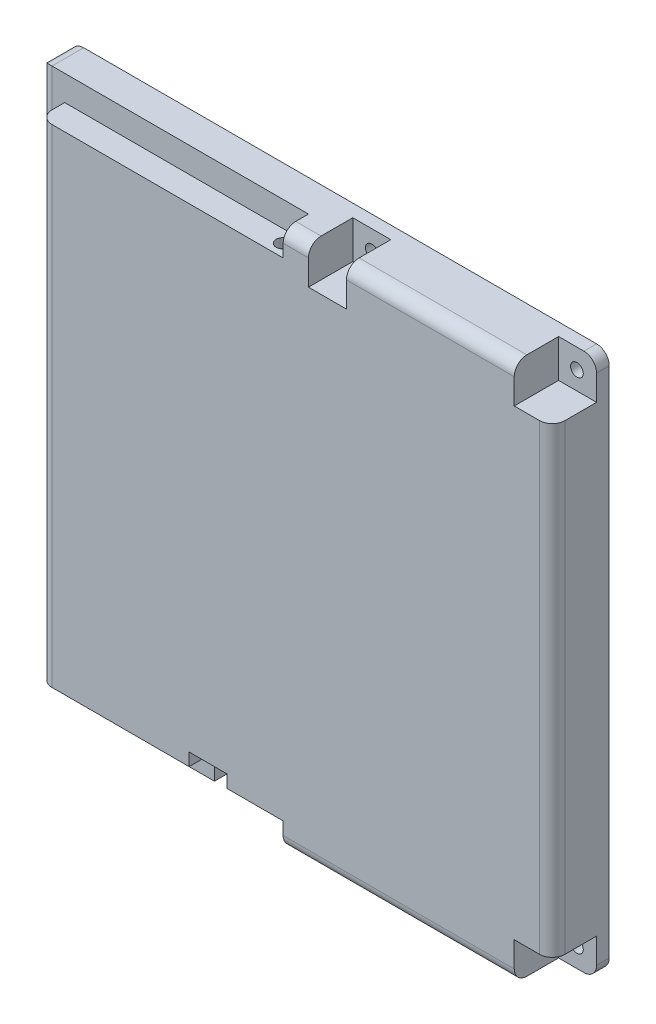
SolidWorks part; units mm, degrees
material "PLA"
ref_plane "前视基准面" through (0, 0, 0) normal (0, 0, 1) x (1, 0, 0)
ref_plane "上视基准面" through (0, 0, 0) normal (0, 1, 0) x (1, 0, 0)
ref_plane "右视基准面" through (0, 0, 0) normal (1, 0, 0) x (0, 0, -1)
sketch "草图1" plane through (0, 0, 0) normal (0, 0, 1) x (1, 0, 0)
  line L2 (70.4448, 16.0581) -> (70.4448, -68.9419)
  line L3 (70.4448, -68.9419) -> (155.4453, -68.9419)
  line L4 (70.4448, 16.0581) -> (155.4448, 16.0581)
  line L5 (155.4448, 16.0581) -> (155.4453, 16.0581)
  line L8 (155.4453, 16.0581) -> (155.4453, -68.9419)
  dimension "D1" = 85
  dimension "D2" = 85
extrude "凸台-拉伸1" add sketch "草图1" along normal blind 9
sketch "草图4" plane through (0, 0, 9) normal (0, 0, 1) x (1, 0, 0)
  line L1 (112.9451, 16.0581) -> (70.4448, 16.0581)
  line L6 (70.4448, 16.0581) -> (70.4448, -68.9419)
  line L10 (112.9451, -68.9419) -> (112.9451, 16.0581) construction
  line L11 (70.4448, -68.9419) -> (155.4453, -68.9419) construction
  line L13 (70.4448, -68.9419) -> (112.9451, -68.9419)
  line L14 (112.9451, -68.9419) -> (112.9451, -64.9419)
  line L15 (112.9451, -64.9419) -> (74.4448, -64.9419)
  line L16 (74.4448, -64.9419) -> (74.4448, 12.0581)
  line L17 (74.4448, 12.0581) -> (112.9451, 12.0581)
  line L18 (112.9451, 12.0581) -> (112.9451, 16.0581)
  dimension "D1" = 4
  dimension "D2" = 4
  dimension "D3" = 4
extrude "支架切除-拉伸2" cut sketch "草图4" against normal blind 4
sketch "草图7" plane through (0, 0, 9) normal (0, 0, 1) x (1, 0, 0)
  line L0 (155.4453, -26.4419) -> (112.9448, -26.4419) construction
  line L1 (155.4453, 16.0581) -> (149.4453, 16.0581)
  line L2 (155.4453, 16.0581) -> (155.4453, 10.0581)
  line L3 (155.4453, 10.0581) -> (149.4453, 10.0581)
  line L4 (149.4453, 16.0581) -> (149.4453, 10.0581)
  line L5 (155.4453, -68.9419) -> (155.4453, 16.0581) construction
  line L6 (149.4453, -68.9419) -> (149.4453, -62.9419)
  line L7 (155.4453, -62.9419) -> (149.4453, -62.9419)
  line L8 (155.4453, -68.9419) -> (155.4453, -62.9419)
  line L9 (155.4453, -68.9419) -> (149.4453, -68.9419)
  dimension "D1" = 6
  dimension "D2" = 6
extrude "顶螺丝切除-拉伸4" cut sketch "草图7" against normal blind 7
sketch "草图10" plane through (0, 0, 9) normal (0, 0, 1) x (1, 0, 0)
  line L0 (149.4453, 16.0581) -> (112.9451, 16.0581) construction
  line L1 (116.9448, 16.0581) -> (122.9448, 16.0581)
  line L2 (155.4453, -68.9419) -> (155.4453, -62.9419) construction
  line L3 (149.4453, -68.9419) -> (155.4453, -68.9419) construction
  line L4 (155.4453, -62.9419) -> (149.4453, -62.9419) construction
  line L5 (149.4453, -62.9419) -> (149.4453, -68.9419) construction
  line L6 (155.4453, 10.0581) -> (155.4453, 16.0581) construction
  line L7 (155.4453, 16.0581) -> (149.4453, 16.0581) construction
  line L8 (149.4453, 16.0581) -> (149.4453, 10.0581) construction
  line L9 (149.4453, 10.0581) -> (155.4453, 10.0581) construction
  line L10 (155.4453, -68.9419) -> (155.4453, -62.9419) construction
  line L11 (149.4453, -68.9419) -> (155.4453, -68.9419) construction
  line L12 (155.4453, -62.9419) -> (149.4453, -62.9419) construction
  line L13 (149.4453, -62.9419) -> (149.4453, -68.9419) construction
  line L14 (155.4453, 10.0581) -> (155.4453, 16.0581) construction
  line L15 (155.4453, 16.0581) -> (149.4453, 16.0581) construction
  line L16 (149.4453, 16.0581) -> (149.4453, 10.0581) construction
  line L17 (149.4453, 10.0581) -> (155.4453, 10.0581) construction
  line L18 (116.9448, 16.0581) -> (116.9448, 10.0581)
  line L19 (116.9448, 10.0581) -> (122.9448, 10.0581)
  line L20 (122.9448, 16.0581) -> (122.9448, 10.0581)
  line L22 (98.0948, -62.9419) -> (104.0948, -62.9419)
  line L23 (98.0948, -62.9419) -> (98.0948, -68.9419)
  line L24 (98.0948, -68.9419) -> (104.0948, -68.9419)
  line L25 (104.0948, -62.9419) -> (104.0948, -68.9419)
  line L28 (98.0948, -65.9419) -> (104.0948, -65.9419) construction
  line L30 (101.0948, -68.9419) -> (101.0948, -62.9419) construction
  line L31 (70.4448, -68.9419) -> (112.9451, -68.9419) construction
  circle A2 centre (101.0948, -65.8419) radius 0.825 construction
  circle A3 centre (119.9448, 12.9581) radius 0.825 construction
  dimension "D5" = 3
  dimension "D6" = 3
  dimension "D1" = 6
  dimension "D2" = 6
  dimension "D3" = 6
  dimension "D4" = 6
extrude "底螺丝切除-拉伸6" cut sketch "草图10" against normal blind 7
shell "抽壳1" thickness 1.5
sketch "草图5" plane through (0, 12.0581, 0) normal (0, 1, 0) x (1, 0, 0)
  line L0 (112.9451, -5) -> (70.4448, -5) construction
  line L2 (112.9451, -5) -> (112.9451, -9) construction
  circle A1 centre (110.9451, -7) radius 1 construction
  circle A2 centre (110.9451, -7) radius 1.1
  dimension "D1" = 2.2
  dimension "D2" = 2
  dimension "D3" = 2
extrude "切除-拉伸3" cut sketch "草图5" against normal blind 4
ref_plane "基准面1" through (0, -26.4419, 0) normal (0, 1, 0) x (1, 0, 0)
mirror "镜向1" about plane through (0, -26.4419, 0) normal (0, 1, 0) of "切除-拉伸3"
sketch "草图6" plane through (0, 0, 9) normal (0, 0, 1) x (1, 0, 0)
  circle A0 centre (152.3448, 12.9581) radius 1
  circle A1 centre (152.3448, -65.8419) radius 1
  dimension "D1" = 2
  dimension "D2" = 2
extrude "顶螺丝切除-拉伸5" cut sketch "草图6" against normal up to next from surface
fillet "圆角1" radius 2 10 edges at (131.1952, -68.9419, 9) (114.9449, 16.0581, 9) (70.4448, 16.0581, 2.5) (70.4448, -68.9419, 2.5) (155.4453, -68.9419, 1) (155.4453, 16.0581, 1) (155.4453, -26.4419, 9) (74.4448, -26.4419, 9) (70.4448, -26.4419, 5) (136.1951, 16.0581, 9)
sketch "草图12" plane through (0, 0, 2) normal (0, 0, 1) x (1, 0, 0)
  circle A0 centre (119.9448, 12.9581) radius 1
  circle A3 centre (101.0948, -65.8419) radius 1
  dimension "D1" = 2
extrude "底螺丝切除-拉伸7" cut sketch "草图12" against normal up to next
